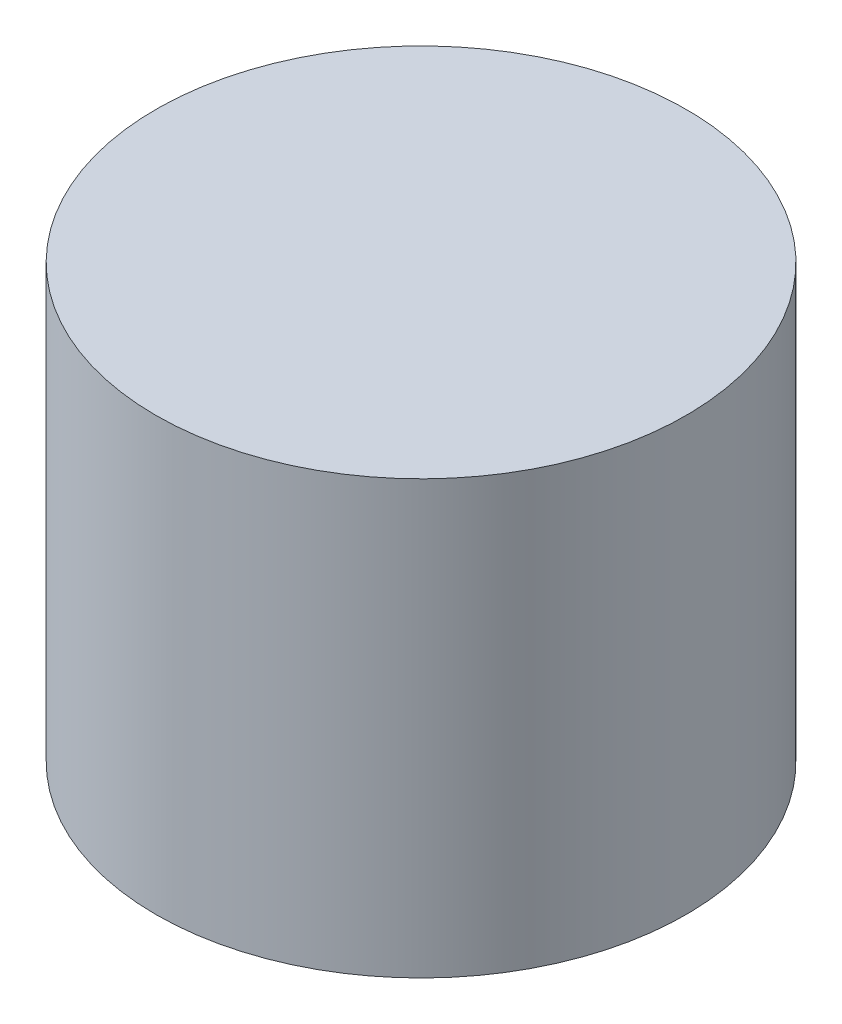
SolidWorks part; units mm, degrees
ref_plane "Front Plane" through (0, 0, 0) normal (0, 0, 1) x (1, 0, 0)
ref_plane "Top Plane" through (0, 0, 0) normal (0, 1, 0) x (1, 0, 0)
ref_plane "Right Plane" through (0, 0, 0) normal (1, 0, 0) x (0, 0, -1)
sketch "Sketch1" plane through (0, 0, 0) normal (0, 1, 0) x (1, 0, 0)
  circle A0 centre (0, 0) radius 37.5
  dimension "D1" = 75
extrude "Boss-Extrude1" add sketch "Sketch1" along normal blind 61.15
